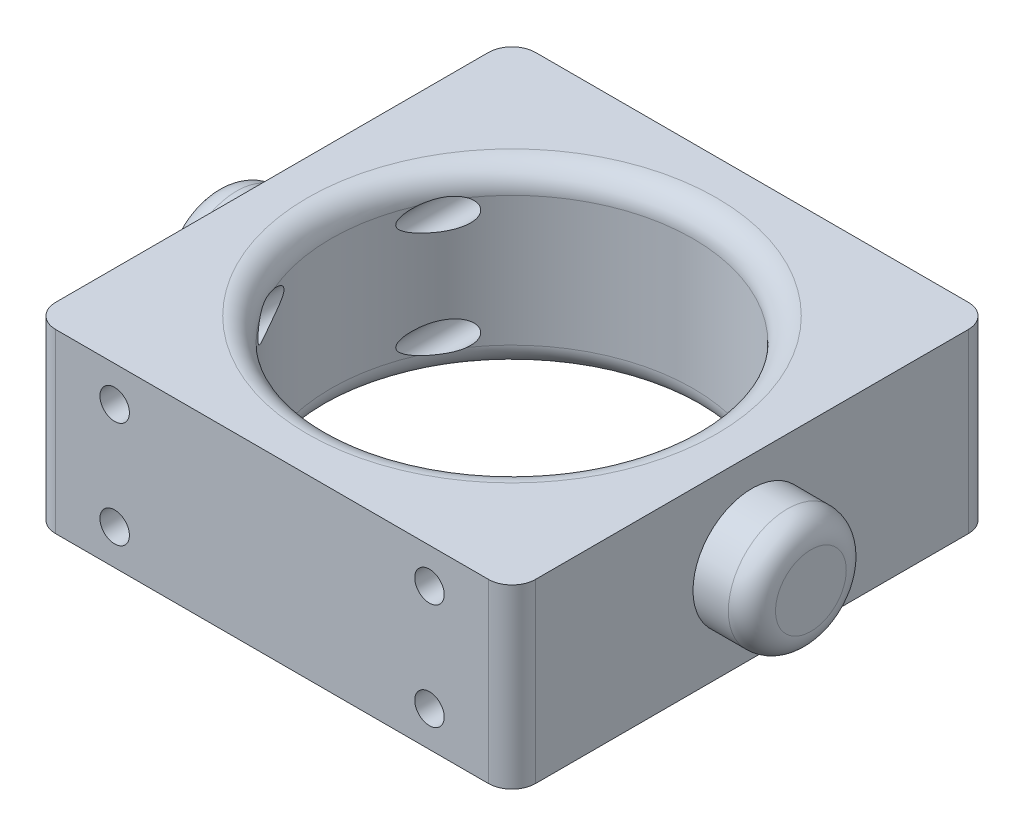
SolidWorks part; units mm, degrees
ref_plane "Front Plane" through (0, 0, 0) normal (0, 0, 1) x (1, 0, 0)
ref_plane "Top Plane" through (0, 0, 0) normal (0, 1, 0) x (1, 0, 0)
ref_plane "Right Plane" through (0, 0, 0) normal (1, 0, 0) x (0, 0, -1)
sketch "Sketch1" plane through (0, 0, 0) normal (0, 1, 0) x (1, 0, 0)
  line L1 (-20.35, -20.35) -> (20.35, -20.35)
  line L2 (-20.35, -20.35) -> (-20.35, 20.35)
  line L3 (-20.35, 20.35) -> (20.35, 20.35)
  line L4 (20.35, -20.35) -> (20.35, 20.35)
  line L5 (-20.35, -20.35) -> (20.35, 20.35) construction
  line L6 (-20.35, 20.35) -> (20.35, -20.35) construction
  circle A0 centre (0, 0) radius 15.35
  point P0 (0, 0)
  dimension "D3" = 30.7
  dimension "D1" = 40.7
  dimension "D2" = 40.7
extrude "Boss-Extrude1" add sketch "Sketch1" along normal blind 15
sketch "Sketch2" plane through (-20.35, 0, 0) normal (-1, 0, 0) x (0, 0, 1)
  line L0 (20.35, 7.5) -> (-20.35, 7.5) construction
  line L1 (20.35, 15) -> (20.35, 0) construction
  line L2 (-20.35, 15) -> (-20.35, 0) construction
  line L3 (0, 0) -> (0, 15) construction
  line L4 (-20.35, 0) -> (20.35, 0) construction
  line L5 (-20.35, 15) -> (20.35, 15) construction
  circle A0 centre (0, 7.5) radius 5
  dimension "D1" = 10
extrude "Boss-Extrude2" add sketch "Sketch2" along normal blind 5
ref_plane "Plane1" through (0, 0, 0) normal (-1, 0, 0) x (0, 0, 1)
mirror "Mirror1" about plane through (0, 0, 0) normal (-1, 0, 0) of "Boss-Extrude2"
fillet "Fillet1" radius 2 6 edges at (20.35, 7.5, 20.35) (-20.35, 7.5, 20.35) (20.35, 7.5, -20.35) (-20.35, 7.5, -20.35) (0, 0, 15.35) (0, 15, 15.35)
fillet "Fillet2" radius 2 2 edges at (25.35, 7.5, 5) (-25.35, 7.5, 5)
hole_wizard "Tap Drill for M3x0.5 Tap1" positions "Sketch4" profile "Sketch3" hole size "M3x0.5" standard "Ansi Metric"
sketch "Sketch4" plane through (0, 0, 20.35) normal (0, 0, 1) x (1, 0, 0)
  line L0 (-18.35, 15) -> (18.35, 15) construction
  line L1 (-18.35, 0) -> (18.35, 0) construction
  line L2 (-18.35, 15) -> (-18.35, 0) construction
  line L3 (18.35, 0) -> (18.35, 15) construction
  point P0 (-13.35, 12)
  point P1 (-13.35, 3)
  point P3 (13.35, 12)
  point P5 (13.35, 3)
  dimension "D1" = 3
  dimension "D2" = 3
  dimension "D3" = 5
  dimension "D4" = 5
  dimension "D5" = 5
  dimension "D6" = 5
  dimension "D7" = 3
  dimension "D8" = 3
sketch "Sketch3" plane through (-13.35, 12, 20.35) normal (1, 0, 0) x (0, -1, 0)
  line L0 (0, 0) -> (0, 21.1001)
  line L1 (0, 21.1001) -> (1.25, 20.349)
  line L2 (1.25, 20.349) -> (1.25, 0)
  line L5 (1.25, 0) -> (0, 0)
  line L10 (0, 21.1001) -> (-1.25, 20.349) construction
  line L11 (0, -6.35) -> (0, 107.95) construction
  dimension "Hole Dia." = 2.5
  dimension "Hole Depth" = 20.349
  dimension "Drill Angle" = 118
hole_wizard "Tap Drill for M3x0.5 Tap2" positions "Sketch8" profile "Sketch7" hole size "M3x0.5" standard "Ansi Metric"
sketch "Sketch8" plane through (0, 0, -20.35) normal (0, 0, -1) x (-1, 0, 0)
  line L0 (-18.35, 15) -> (-18.35, 0) construction
  line L1 (-18.35, 0) -> (18.35, 0) construction
  line L2 (-18.35, 15) -> (18.35, 15) construction
  line L3 (18.35, 0) -> (18.35, 15) construction
  point P0 (-13.35, 12)
  point P1 (-13.35, 3)
  point P3 (13.35, 12)
  point P5 (13.35, 3)
  dimension "D1" = 5
  dimension "D2" = 5
  dimension "D3" = 3
  dimension "D4" = 3
  dimension "D5" = 3
  dimension "D6" = 3
  dimension "D7" = 5
  dimension "D8" = 5
sketch "Sketch7" plane through (13.35, 12, -20.35) normal (1, 0, 0) x (0, 1, 0)
  line L0 (0, 0) -> (0, 21.1011)
  line L1 (0, 21.1011) -> (1.25, 20.35)
  line L2 (1.25, 20.35) -> (1.25, 0)
  line L5 (1.25, 0) -> (0, 0)
  line L10 (0, 21.1011) -> (-1.25, 20.35) construction
  line L11 (0, -6.35) -> (0, 107.95) construction
  dimension "Hole Dia." = 2.5
  dimension "Hole Depth" = 20.35
  dimension "Drill Angle" = 118
